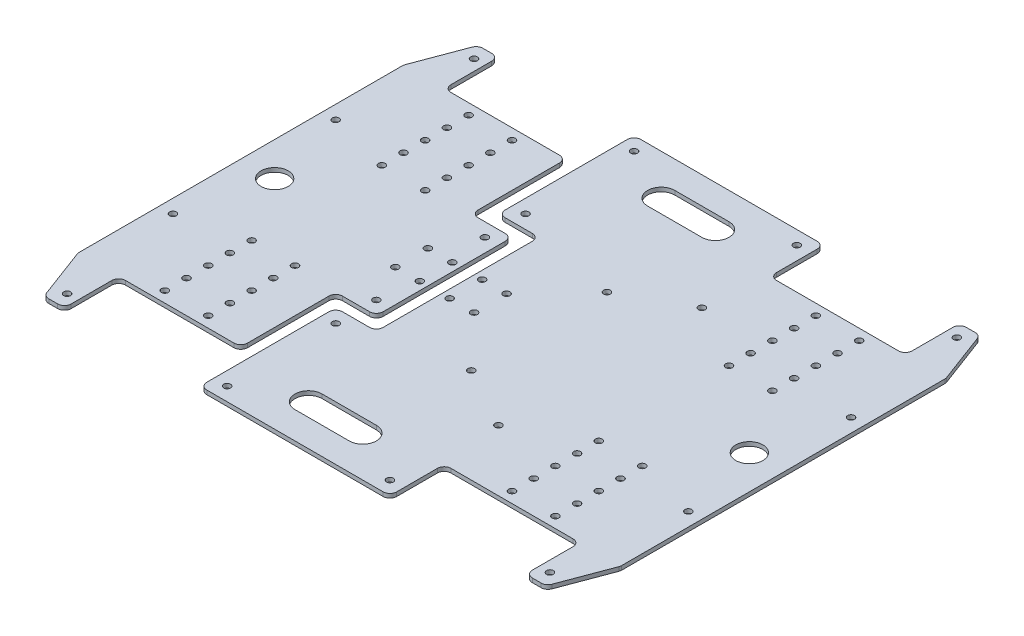
SolidWorks part; units mm, degrees
ref_plane "前视基准面" through (0, 0, 0) normal (0, 0, 1) x (1, 0, 0)
ref_plane "上视基准面" through (0, 0, 0) normal (0, 1, 0) x (1, 0, 0)
ref_plane "右视基准面" through (0, 0, 0) normal (1, 0, 0) x (0, 0, -1)
sketch "草图1" plane through (0, 0, 0) normal (0, 1, 0) x (1, 0, 0)
  line L0 (0, 0) -> (241.3231, 0) construction
  line L1 (0, 0) -> (-261.3933, 0) construction
  line L3 (-200, -119.0933) -> (-200, 119.0933)
  line L4 (-199.6816, 120.8489) -> (-186.2166, 156.7556)
  line L5 (-181.535, 160) -> (-175, 160)
  line L6 (-170, 155) -> (-170, 125)
  line L7 (-165, 120) -> (-85, 120)
  line L8 (-80, 115) -> (-80, 55)
  line L9 (-75, 50) -> (-55, 50)
  line L10 (-50, 45) -> (-50, -45)
  line L11 (-70, 120) -> (-70, 65)
  line L12 (-65, 60) -> (-45, 60)
  line L13 (-40, 55) -> (-40, -55)
  line L14 (-70, 120) -> (-70, 155)
  line L15 (-65, 160) -> (65, 160)
  line L16 (70, 155) -> (70, 125)
  line L17 (75, 120) -> (165, 120)
  line L18 (170, 125) -> (170, 155)
  line L19 (175, 160) -> (181.535, 160)
  line L20 (186.2166, 156.7556) -> (199.6816, 120.8489)
  line L21 (200, 119.0933) -> (200, -119.0933)
  line L22 (-70, 120) -> (-70, 60) construction
  line L23 (-70, 60) -> (-40, 60) construction
  line L24 (-40, 60) -> (-40, 0) construction
  line L25 (-80, 50) -> (-50, 50) construction
  line L26 (-50, 50) -> (-50, 0) construction
  line L27 (-80, 120) -> (-80, 50) construction
  line L28 (-20, 130) -> (20, 130) construction
  line L29 (-20, 140) -> (20, 140)
  line L30 (-20, 120) -> (20, 120)
  line L31 (-20, -130) -> (20, -130) construction
  line L36 (-20, -140) -> (20, -140)
  line L37 (-20, -120) -> (20, -120)
  line L38 (186.2166, -156.7556) -> (199.6816, -120.8489)
  line L39 (175, -160) -> (181.535, -160)
  line L40 (170, -125) -> (170, -155)
  line L41 (75, -120) -> (165, -120)
  line L42 (70, -155) -> (70, -125)
  line L43 (-65, -160) -> (65, -160)
  line L44 (-70, -120) -> (-70, -155)
  line L45 (-65, -60) -> (-45, -60)
  line L46 (-70, -120) -> (-70, -65)
  line L47 (-75, -50) -> (-55, -50)
  line L48 (-80, -115) -> (-80, -55)
  line L49 (-165, -120) -> (-85, -120)
  line L50 (-170, -155) -> (-170, -125)
  line L51 (-181.535, -160) -> (-175, -160)
  line L52 (-199.6816, -120.8489) -> (-186.2166, -156.7556)
  arc A0 (199.6816, 120.8489) -> (200, 119.0933) centre (195, 119.0933) cw
  arc A1 (181.535, 160) -> (186.2166, 156.7556) centre (181.535, 155) cw
  arc A2 (170, 155) -> (175, 160) centre (175, 155) cw
  arc A3 (165, 120) -> (170, 125) centre (165, 125) ccw
  arc A4 (70, 125) -> (75, 120) centre (75, 125) ccw
  arc A5 (65, 160) -> (70, 155) centre (65, 155) cw
  arc A6 (-70, 155) -> (-65, 160) centre (-65, 155) cw
  arc A7 (-70, 65) -> (-65, 60) centre (-65, 65) ccw
  arc A8 (-45, 60) -> (-40, 55) centre (-45, 55) cw
  arc A9 (-55, 50) -> (-50, 45) centre (-55, 45) cw
  arc A10 (-80, 55) -> (-75, 50) centre (-75, 55) ccw
  arc A11 (-85, 120) -> (-80, 115) centre (-85, 115) cw
  arc A12 (-170, 125) -> (-165, 120) centre (-165, 125) ccw
  arc A13 (-175, 160) -> (-170, 155) centre (-175, 155) cw
  arc A14 (-186.2166, 156.7556) -> (-181.535, 160) centre (-181.535, 155) cw
  arc A15 (-200, 119.0933) -> (-199.6816, 120.8489) centre (-195, 119.0933) cw
  circle A16 centre (-112, 112) radius 2.5
  circle A17 centre (-144, 112) radius 2.5
  circle A18 centre (-144, 96) radius 2.5
  circle A19 centre (-144, 80) radius 2.5
  circle A20 centre (-144, 64) radius 2.5
  circle A21 centre (-144, 48) radius 2.5
  circle A22 centre (-112, 96) radius 2.5
  circle A23 centre (-112, 80) radius 2.5
  circle A24 centre (-112, 64) radius 2.5
  circle A25 centre (-112, 48) radius 2.5
  circle A26 centre (112, 112) radius 2.5
  circle A27 centre (144, 112) radius 2.5
  circle A28 centre (144, 96) radius 2.5
  circle A29 centre (144, 80) radius 2.5
  circle A30 centre (144, 64) radius 2.5
  circle A31 centre (144, 48) radius 2.5
  circle A33 centre (112, 96) radius 2.5
  circle A34 centre (112, 80) radius 2.5
  circle A35 centre (112, 64) radius 2.5
  circle A36 centre (112, 48) radius 2.5
  circle A38 centre (-56, 12) radius 2.5
  circle A39 centre (-74, 12) radius 2.5
  circle A40 centre (-34, 12) radius 2.5
  circle A41 centre (-16, 12) radius 2.5
  circle A42 centre (-178, 150) radius 2.5
  circle A43 centre (178, 150) radius 2.5
  circle A44 centre (-60, 150) radius 2.5
  circle A45 centre (60, 150) radius 2.5
  circle A46 centre (-60, 70) radius 2.5
  circle A47 centre (-60, 40) radius 2.5
  circle A48 centre (-190, 60) radius 2.5
  circle A49 centre (190, 60) radius 2.5
  arc A50 (-20, 140) -> (-20, 120) centre (-20, 130) ccw
  arc A51 (20, 120) -> (20, 140) centre (20, 130) ccw
  circle A52 centre (-175, 0) radius 10
  circle A53 centre (175, 0) radius 10
  circle A54 centre (65, 75) radius 2.5
  circle A55 centre (20, 50) radius 2.5
  arc A56 (-20, -140) -> (-20, -120) centre (-20, -130) cw
  arc A57 (20, -120) -> (20, -140) centre (20, -130) cw
  circle A58 centre (20, -50) radius 2.5
  circle A59 centre (65, -75) radius 2.5
  circle A60 centre (190, -60) radius 2.5
  circle A61 centre (-190, -60) radius 2.5
  circle A62 centre (-60, -40) radius 2.5
  circle A63 centre (-60, -70) radius 2.5
  circle A64 centre (60, -150) radius 2.5
  circle A65 centre (-60, -150) radius 2.5
  circle A66 centre (178, -150) radius 2.5
  circle A67 centre (-178, -150) radius 2.5
  circle A68 centre (-16, -12) radius 2.5
  circle A69 centre (-34, -12) radius 2.5
  circle A70 centre (-74, -12) radius 2.5
  circle A71 centre (-56, -12) radius 2.5
  circle A72 centre (112, -48) radius 2.5
  circle A73 centre (112, -64) radius 2.5
  circle A74 centre (112, -80) radius 2.5
  circle A75 centre (112, -96) radius 2.5
  circle A76 centre (144, -48) radius 2.5
  circle A77 centre (144, -64) radius 2.5
  circle A78 centre (144, -80) radius 2.5
  circle A79 centre (144, -96) radius 2.5
  circle A80 centre (144, -112) radius 2.5
  circle A81 centre (112, -112) radius 2.5
  circle A82 centre (-112, -48) radius 2.5
  circle A83 centre (-112, -64) radius 2.5
  circle A84 centre (-112, -80) radius 2.5
  circle A85 centre (-112, -96) radius 2.5
  circle A86 centre (-144, -48) radius 2.5
  circle A87 centre (-144, -64) radius 2.5
  circle A88 centre (-144, -80) radius 2.5
  circle A89 centre (-144, -96) radius 2.5
  circle A90 centre (-144, -112) radius 2.5
  circle A91 centre (-112, -112) radius 2.5
  arc A92 (-200, -119.0933) -> (-199.6816, -120.8489) centre (-195, -119.0933) ccw
  arc A93 (-186.2166, -156.7556) -> (-181.535, -160) centre (-181.535, -155) ccw
  arc A94 (-175, -160) -> (-170, -155) centre (-175, -155) ccw
  arc A95 (-170, -125) -> (-165, -120) centre (-165, -125) cw
  arc A96 (-85, -120) -> (-80, -115) centre (-85, -115) ccw
  arc A97 (-80, -55) -> (-75, -50) centre (-75, -55) cw
  arc A98 (-55, -50) -> (-50, -45) centre (-55, -45) ccw
  arc A99 (-45, -60) -> (-40, -55) centre (-45, -55) ccw
  arc A100 (-70, -65) -> (-65, -60) centre (-65, -65) cw
  arc A101 (-70, -155) -> (-65, -160) centre (-65, -155) ccw
  arc A102 (65, -160) -> (70, -155) centre (65, -155) ccw
  arc A103 (70, -125) -> (75, -120) centre (75, -125) cw
  arc A104 (165, -120) -> (170, -125) centre (165, -125) cw
  arc A105 (170, -155) -> (175, -160) centre (175, -155) ccw
  arc A106 (181.535, -160) -> (186.2166, -156.7556) centre (181.535, -155) ccw
  arc A107 (199.6816, -120.8489) -> (200, -119.0933) centre (195, -119.0933) ccw
  point P2 (-200, -120)
  point P27 (200, 120)
  point P30 (185, 160)
  point P33 (170, 160)
  point P36 (170, 120)
  point P39 (70, 120)
  point P42 (70, 160)
  point P62 (-170, 120)
  point P65 (-170, 160)
  point P68 (-185, 160)
  point P71 (-200, 120)
  point P138 (0, 130)
  point P152 (0, -130)
  point P275 (200, 0)
  point P276 (-200, 0)
  point P277 (-185, -160)
  point P278 (-170, -160)
  point P279 (-170, -120)
  point P280 (70, -160)
  point P281 (70, -120)
  point P282 (170, -120)
  point P283 (170, -160)
  point P284 (185, -160)
  point P285 (200, -120)
  dimension "D11" = 5
  dimension "D18" = 5
  dimension "D23" = 5
  dimension "D28" = 5
  dimension "D34" = 5
  dimension "D36" = 5
  dimension "D39" = 5
  dimension "D42" = 5
  dimension "D45" = 5
  dimension "D48" = 5
  dimension "D51" = 5
  dimension "D54" = 5
  dimension "D57" = 5
  dimension "D60" = 10
  dimension "D64" = 10
  dimension "D66" = 10
  dimension "D71" = 5
  dimension "D74" = 50
  dimension "D76" = 5
  dimension "D1" = 10
  dimension "D2" = 120
  dimension "D3" = 120
  dimension "D4" = 40
  dimension "D5" = 90
  dimension "D6" = 120
  dimension "D7" = 15
  dimension "D8" = 200
  dimension "D9" = 30
  dimension "D10" = 50
  dimension "D12" = 200
  dimension "D13" = 15
  dimension "D14" = 30
  dimension "D15" = 100
  dimension "D16" = 40
  dimension "D17" = 120
  dimension "D19" = 8
  dimension "D20" = 58
  dimension "D24" = 8
  dimension "D25" = 58
  dimension "D29" = 12
  dimension "D30" = 6
  dimension "D32" = 12
  dimension "D33" = 6
  dimension "D37" = 10
  dimension "D38" = 8
  dimension "D40" = 8
  dimension "D41" = 10
  dimension "D43" = 10
  dimension "D44" = 10
  dimension "D46" = 10
  dimension "D47" = 10
  dimension "D49" = 10
  dimension "D50" = 10
  dimension "D52" = 10
  dimension "D53" = 10
  dimension "D55" = 10
  dimension "D56" = 60
  dimension "D58" = 10
  dimension "D59" = 60
  dimension "D61" = 30
  dimension "D62" = 50
  dimension "D63" = 50
  dimension "D65" = 25
  dimension "D67" = 25
  dimension "D70" = 85
  dimension "D72" = 5
  dimension "D75" = 50
  dimension "D21" = 2
  dimension "D22" = 5
  dimension "D26" = 2
  dimension "D27" = 5
  dimension "D31" = 2
  dimension "D35" = 2
extrude "凸台-拉伸1" add sketch "草图1" along normal blind 3
